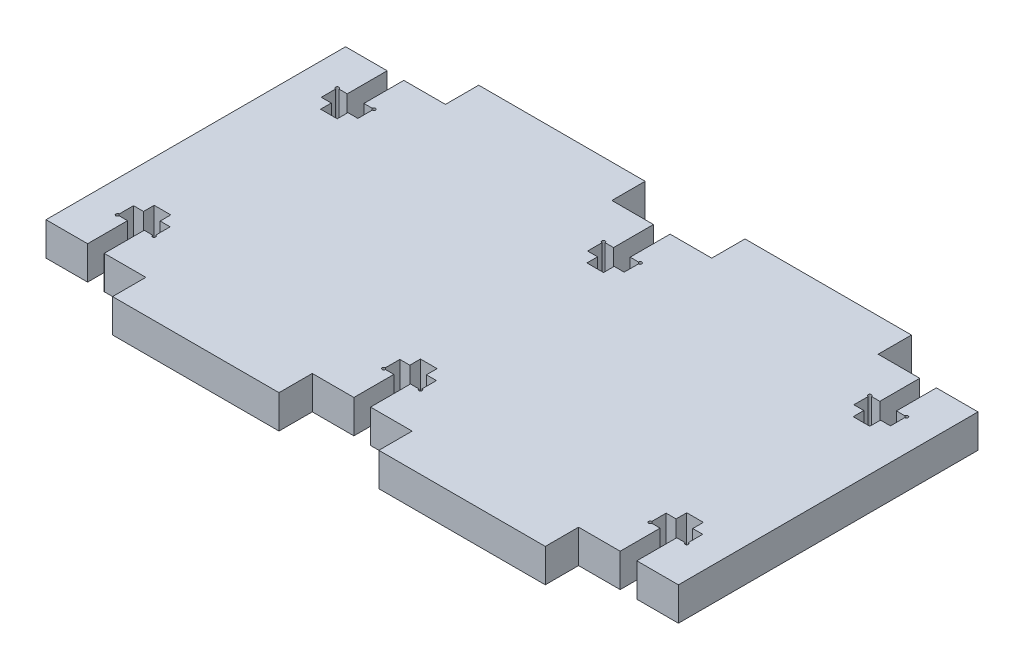
SolidWorks part; units mm, degrees
material "PVC rigido"
ref_plane "Piano frontale" through (0, 0, 0) normal (0, 0, 1) x (1, 0, 0)
ref_plane "Piano superiore" through (0, 0, 0) normal (0, 1, 0) x (1, 0, 0)
ref_plane "Piano destro" through (0, 0, 0) normal (1, 0, 0) x (0, 0, -1)
sketch "Schizzo1" plane through (0, 0, 0) normal (0, 1, 0) x (1, 0, 0)
  line L1 (-54.5649, -28.2811) -> (40.4351, -28.2811)
  line L2 (-54.5649, -28.2811) -> (-54.5649, 26.7189)
  line L3 (-54.5649, 26.7189) -> (40.4351, 26.7189)
  line L4 (40.4351, -28.2811) -> (40.4351, 26.7189)
  dimension "D1" = 95
  dimension "D2" = 55
sketch "Schizzo2" plane through (0, 0, 0) normal (0, 1, 0) x (1, 0, 0)
  line L0 (-54.5649, -0.7811) -> (40.4351, -0.7811) construction
  line L1 (-54.5649, -28.2811) -> (-39.5649, -28.2811)
  line L2 (-54.5649, -28.2811) -> (-54.5649, -23.2811)
  line L3 (-54.5649, -23.2811) -> (-39.5649, -23.2811)
  line L4 (-39.5649, -28.2811) -> (-39.5649, -23.2811)
  line L5 (-54.5649, -28.2811) -> (-54.5649, 26.7189) construction
  line L6 (40.4351, -28.2811) -> (40.4351, 26.7189) construction
  line L7 (-7.0649, -28.2811) -> (-7.0649, 26.7189) construction
  line L8 (-54.5649, -28.2811) -> (40.4351, -28.2811) construction
  line L9 (-54.5649, 26.7189) -> (40.4351, 26.7189) construction
  line L10 (-54.5649, 26.7189) -> (-54.5649, 21.7189)
  line L11 (-54.5649, 26.7189) -> (-39.5649, 26.7189)
  line L12 (-39.5649, 26.7189) -> (-39.5649, 21.7189)
  line L13 (-54.5649, 21.7189) -> (-39.5649, 21.7189)
  line L14 (40.4351, -28.2811) -> (40.4351, -23.2811)
  line L15 (40.4351, -28.2811) -> (25.4351, -28.2811)
  line L16 (25.4351, -28.2811) -> (25.4351, -23.2811)
  line L17 (40.4351, -23.2811) -> (25.4351, -23.2811)
  line L18 (40.4351, 26.7189) -> (40.4351, 21.7189)
  line L19 (40.4351, 26.7189) -> (25.4351, 26.7189)
  line L20 (25.4351, 26.7189) -> (25.4351, 21.7189)
  line L21 (40.4351, 21.7189) -> (25.4351, 21.7189)
  line L22 (-14.5649, -28.2811) -> (0.4351, -28.2811)
  line L23 (-14.5649, -28.2811) -> (-14.5649, -23.2811)
  line L24 (-14.5649, -23.2811) -> (0.4351, -23.2811)
  line L25 (0.4351, -28.2811) -> (0.4351, -23.2811)
  line L26 (-14.5649, 26.7189) -> (-14.5649, 21.7189)
  line L27 (-14.5649, 21.7189) -> (0.4351, 21.7189)
  line L28 (0.4351, 26.7189) -> (0.4351, 21.7189)
  line L29 (-14.5649, 26.7189) -> (0.4351, 26.7189)
  point P33 (-7.0649, -23.2811)
  dimension "D1" = 15
  dimension "D2" = 5
  dimension "D3" = 15
  dimension "D4" = 5
extrude "Estrusione-Estrusione2" add sketch "Schizzo1" against normal blind 5
extrude "Taglio-Estrusione1" cut sketch "Schizzo2" against normal through all
sketch "Schizzo3" plane through (0, 0, 0) normal (0, 1, 0) x (1, 0, 0)
  line L0 (-48.3149, -23.2811) -> (-45.8149, -23.2811)
  line L1 (-8.3149, -23.2811) -> (-5.8149, -23.2811)
  line L2 (-54.5649, -0.7811) -> (40.4351, -0.7811) construction
  line L3 (-54.5649, 21.7189) -> (-54.5649, -23.2811) construction
  line L4 (-48.3149, -23.2811) -> (-48.3149, -17.2811)
  line L5 (-48.3149, -17.2811) -> (-49.8149, -17.2811)
  line L6 (-49.8149, -17.2811) -> (-49.8149, -14.8811)
  line L7 (-49.8149, -14.8811) -> (-48.3149, -14.8811)
  line L8 (-48.3149, -14.8811) -> (-48.3149, -13.2811)
  line L9 (-48.3149, -13.2811) -> (-45.8149, -13.2811)
  line L10 (-45.8149, -13.2811) -> (-45.8149, -14.8811)
  line L11 (-45.8149, -14.8811) -> (-44.3149, -14.8811)
  line L12 (-44.3149, -14.8811) -> (-44.3149, -17.2811)
  line L13 (-44.3149, -17.2811) -> (-45.8149, -17.2811)
  line L14 (-45.8149, -17.2811) -> (-45.8149, -23.2811)
  line L15 (40.4351, -23.2811) -> (40.4351, 21.7189) construction
  line L16 (-47.0649, 21.7189) -> (-47.0649, -23.2811) construction
  line L17 (-54.5649, 21.7189) -> (-39.5649, 21.7189) construction
  line L18 (-39.5649, -23.2811) -> (-54.5649, -23.2811) construction
  line L19 (-7.0649, 21.7189) -> (-7.0649, -23.2811) construction
  line L20 (-14.5649, 21.7189) -> (0.4351, 21.7189) construction
  line L21 (0.4351, -23.2811) -> (-14.5649, -23.2811) construction
  line L22 (32.9351, 21.7189) -> (32.9351, -23.2811) construction
  line L23 (25.4351, 21.7189) -> (40.4351, 21.7189) construction
  line L24 (40.4351, -23.2811) -> (25.4351, -23.2811) construction
  line L25 (31.6851, -23.2811) -> (34.1851, -23.2811)
  line L26 (-8.3149, -23.2811) -> (-8.3149, -17.2811)
  line L27 (-8.3149, -17.2811) -> (-9.8149, -17.2811)
  line L28 (-9.8149, -17.2811) -> (-9.8149, -14.8811)
  line L29 (-9.8149, -14.8811) -> (-8.3149, -14.8811)
  line L30 (-8.3149, -14.8811) -> (-8.3149, -13.2811)
  line L31 (-8.3149, -13.2811) -> (-5.8149, -13.2811)
  line L32 (-5.8149, -13.2811) -> (-5.8149, -14.8811)
  line L33 (-5.8149, -14.8811) -> (-4.3149, -14.8811)
  line L34 (-4.3149, -14.8811) -> (-4.3149, -17.2811)
  line L35 (-4.3149, -17.2811) -> (-5.8149, -17.2811)
  line L36 (-5.8149, -17.2811) -> (-5.8149, -23.2811)
  line L37 (31.6851, 11.7189) -> (34.1851, 11.7189)
  line L38 (31.6851, -23.2811) -> (31.6851, -17.2811)
  line L39 (31.6851, -17.2811) -> (30.1851, -17.2811)
  line L40 (30.1851, -17.2811) -> (30.1851, -14.8811)
  line L41 (30.1851, -14.8811) -> (31.6851, -14.8811)
  line L42 (31.6851, -14.8811) -> (31.6851, -13.2811)
  line L43 (31.6851, -13.2811) -> (34.1851, -13.2811)
  line L44 (34.1851, -13.2811) -> (34.1851, -14.8811)
  line L45 (34.1851, -14.8811) -> (35.6851, -14.8811)
  line L46 (35.6851, -14.8811) -> (35.6851, -17.2811)
  line L47 (35.6851, -17.2811) -> (34.1851, -17.2811)
  line L48 (34.1851, -17.2811) -> (34.1851, -23.2811)
  line L49 (31.6851, 13.3189) -> (31.6851, 11.7189)
  line L50 (30.1851, 13.3189) -> (31.6851, 13.3189)
  line L51 (30.1851, 15.7189) -> (30.1851, 13.3189)
  line L52 (31.6851, 15.7189) -> (30.1851, 15.7189)
  line L53 (31.6851, 21.7189) -> (31.6851, 15.7189)
  line L54 (31.6851, 21.7189) -> (34.1851, 21.7189)
  line L55 (34.1851, 15.7189) -> (34.1851, 21.7189)
  line L56 (35.6851, 15.7189) -> (34.1851, 15.7189)
  line L57 (35.6851, 13.3189) -> (35.6851, 15.7189)
  line L58 (34.1851, 13.3189) -> (35.6851, 13.3189)
  line L59 (34.1851, 11.7189) -> (34.1851, 13.3189)
  line L60 (-8.3149, 11.7189) -> (-5.8149, 11.7189)
  line L61 (-8.3149, 13.3189) -> (-8.3149, 11.7189)
  line L62 (-9.8149, 13.3189) -> (-8.3149, 13.3189)
  line L63 (-9.8149, 15.7189) -> (-9.8149, 13.3189)
  line L64 (-8.3149, 15.7189) -> (-9.8149, 15.7189)
  line L65 (-8.3149, 21.7189) -> (-8.3149, 15.7189)
  line L66 (-8.3149, 21.7189) -> (-5.8149, 21.7189)
  line L67 (-5.8149, 15.7189) -> (-5.8149, 21.7189)
  line L68 (-4.3149, 15.7189) -> (-5.8149, 15.7189)
  line L69 (-4.3149, 13.3189) -> (-4.3149, 15.7189)
  line L70 (-5.8149, 13.3189) -> (-4.3149, 13.3189)
  line L71 (-5.8149, 11.7189) -> (-5.8149, 13.3189)
  line L72 (-48.3149, 11.7189) -> (-45.8149, 11.7189)
  line L73 (-48.3149, 13.3189) -> (-48.3149, 11.7189)
  line L74 (-49.8149, 13.3189) -> (-48.3149, 13.3189)
  line L75 (-49.8149, 15.7189) -> (-49.8149, 13.3189)
  line L76 (-48.3149, 15.7189) -> (-49.8149, 15.7189)
  line L77 (-48.3149, 21.7189) -> (-48.3149, 15.7189)
  line L78 (-48.3149, 21.7189) -> (-45.8149, 21.7189)
  line L79 (-45.8149, 15.7189) -> (-45.8149, 21.7189)
  line L80 (-44.3149, 15.7189) -> (-45.8149, 15.7189)
  line L81 (-44.3149, 13.3189) -> (-44.3149, 15.7189)
  line L82 (-45.8149, 13.3189) -> (-44.3149, 13.3189)
  line L83 (-45.8149, 11.7189) -> (-45.8149, 13.3189)
  line L84 (-39.5649, 21.7189) -> (-39.5649, 26.7189) construction
  line L85 (-14.5649, 26.7189) -> (-14.5649, 21.7189) construction
  line L86 (0.4351, 21.7189) -> (0.4351, 26.7189) construction
  line L87 (25.4351, 26.7189) -> (25.4351, 21.7189) construction
  point P36 (-47.0649, -23.2811)
  point P53 (-7.0649, -23.2811)
  point P66 (32.9351, -23.2811)
  point P99 (-39.5649, 24.2189)
  point P102 (-14.5649, 24.2189)
  point P107 (25.4351, 24.2189)
  point P110 (0.4351, 24.2189)
  dimension "D2" = 2.5
  dimension "D3" = 2.4
  dimension "D4" = 6
  dimension "D5" = 5.5
  dimension "D6" = 40
  dimension "D7" = 40
  dimension "D8" = 2.5
  dimension "D9" = 6
  dimension "D10" = 10
  dimension "D11" = 2.4
  dimension "D12" = 5.5
  dimension "D13" = 2.5
  dimension "D14" = 6
  dimension "D15" = 10
  dimension "D16" = 2.4
  dimension "D17" = 5.5
  dimension "D18" = 25
  dimension "D19" = 25
  dimension "D20" = 10
extrude "Taglio-Estrusione3" cut sketch "Schizzo3" against normal through all
sketch "Schizzo4" plane through (0, 0, 0) normal (0, 1, 0) x (1, 0, 0)
  line L0 (-54.5649, -0.7811) -> (40.4351, -0.7811) construction
  line L1 (-54.5649, 21.7189) -> (-54.5649, -23.2811) construction
  line L2 (40.4351, -23.2811) -> (40.4351, 21.7189) construction
  circle A0 centre (-49.8149, -17.2811) radius 0.25
  circle A1 centre (-44.3149, -17.2811) radius 0.25
  circle A2 centre (-9.8149, -17.2811) radius 0.25
  circle A3 centre (-4.3149, -17.2811) radius 0.25
  circle A4 centre (30.1851, -17.2811) radius 0.25
  circle A5 centre (35.6851, -17.2811) radius 0.25
  circle A6 centre (-49.8149, 15.7189) radius 0.25
  circle A7 centre (-44.3149, 15.7189) radius 0.25
  circle A8 centre (-9.8149, 15.7189) radius 0.25
  circle A9 centre (-4.3149, 15.7189) radius 0.25
  circle A10 centre (30.1851, 15.7189) radius 0.25
  circle A11 centre (35.6851, 15.7189) radius 0.25
  dimension "D1" = 0.5
  dimension "D2" = 0.5
  dimension "D3" = 0.5
extrude "Taglio-Estrusione4" cut sketch "Schizzo4" against normal blind 10
